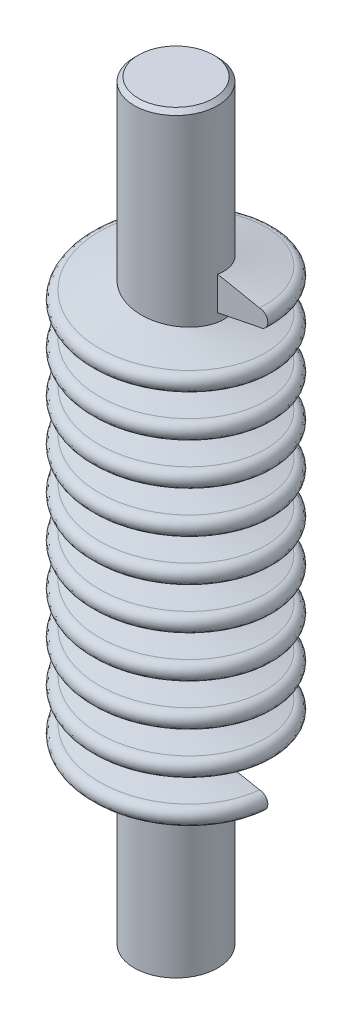
SolidWorks part; units mm, degrees
ref_plane "Front Plane" through (0, 0, 0) normal (0, 0, 1) x (1, 0, 0)
ref_plane "Top Plane" through (0, 0, 0) normal (0, 1, 0) x (1, 0, 0)
ref_plane "Right Plane" through (0, 0, 0) normal (1, 0, 0) x (0, 0, -1)
sketch "Sketch1" plane through (0, 0, 0) normal (0, 1, 0) x (1, 0, 0)
  circle A0 centre (0, 0) radius 5
  dimension "D1" = 10
extrude "Boss-Extrude2" add sketch "Sketch1" along normal blind 90
chamfer "Chamfer1" distance 0.5 angle 45 1 edges at (0, 90, 5)
ref_plane "Plane1" through (0, 70, 0) normal (0, 1, 0) x (1, 0, 0)
sketch "Sketch3" plane through (0, 70, 0) normal (0, 1, 0) x (1, 0, 0)
  circle A0 centre (0, 0) radius 5 construction
  circle A1 centre (0, 0) radius 5
curve "Helix/Spiral1" pitch 5 height 50 turns 10
sketch "Sketch4" plane through (0, 0, 0) normal (0, 0, 1) x (1, 0, 0)
  line L0 (5, 70) -> (6.3876, 70) construction
  line L1 (4.95, 70) -> (-4.95, 70) construction
  line L2 (5, 0) -> (5, 89.5) construction
  line L3 (4.781, 72) -> (5, 72)
  line L4 (4.781, 72) -> (4.781, 68)
  line L5 (4.781, 68) -> (5, 68)
  line L7 (5, 72) -> (10, 71)
  line L8 (5, 68) -> (10, 69)
  arc A0 (10, 69) -> (10, 71) centre (10, 70) ccw
  spline S0 degree 3 poles (5, 70) (5, 69.8965) (4.7397, 69.6872) (3.6276, 69.3751) (1.9632, 69.0625) (0, 68.75) (-1.9632, 68.4375) (-3.6276, 68.125) (-4.7397, 67.8125) (-5.1302, 67.5) (-4.7397, 67.1875) (-3.6276, 66.875) (-1.4084, 66.4583) (1.4084, 66.0417) (3.6276, 65.625) (4.7397, 65.3125) (5.1302, 65) (4.7397, 64.6875) (3.6276, 64.375) (1.4084, 63.9583) (-1.4084, 63.5417) (-3.6276, 63.125) (-4.7397, 62.8125) (-5.1302, 62.5) (-4.7397, 62.1875) (-3.6276, 61.875) (-1.4084, 61.4583) (1.4084, 61.0417) (3.6276, 60.625) (4.7397, 60.3125) (5.1302, 60) (4.7397, 59.6875) (3.6276, 59.375) (1.4084, 58.9583) (-1.4084, 58.5417) (-3.6276, 58.125) (-4.7397, 57.8125) (-5.1302, 57.5) (-4.7397, 57.1875) (-3.6276, 56.875) (-1.4084, 56.4583) (1.4084, 56.0417) (3.6276, 55.625) (4.7397, 55.3125) (5.1302, 55) (4.7397, 54.6875) (3.6276, 54.375) (1.4084, 53.9583) (-1.4084, 53.5417) (-3.6276, 53.125) (-4.7397, 52.8125) (-5.1302, 52.5) (-4.7397, 52.1875) (-3.6276, 51.875) (-1.4084, 51.4583) (1.4084, 51.0417) (3.6276, 50.625) (4.7397, 50.3125) (5.1302, 50) (4.7397, 49.6875) (3.6276, 49.375) (1.4084, 48.9583) (-1.4084, 48.5417) (-3.6276, 48.125) (-4.7397, 47.8125) (-5.1302, 47.5) (-4.7397, 47.1875) (-3.6276, 46.875) (-1.4084, 46.4583) (1.4084, 46.0417) (3.6276, 45.625) (4.7397, 45.3125) (5.1302, 45) (4.7397, 44.6875) (3.6276, 44.375) (1.4084, 43.9583) (-1.4084, 43.5417) (-3.6276, 43.125) (-4.7397, 42.8125) (-5.1302, 42.5) (-4.7397, 42.1875) (-3.6276, 41.875) (-1.4084, 41.4583) (1.4084, 41.0417) (3.6276, 40.625) (4.7397, 40.3125) (5.1302, 40) (4.7397, 39.6875) (3.6276, 39.375) (1.4084, 38.9583) (-1.4084, 38.5417) (-3.6276, 38.125) (-4.7397, 37.8125) (-5.1302, 37.5) (-4.7397, 37.1875) (-3.6276, 36.875) (-1.4084, 36.4583) (1.4084, 36.0417) (3.6276, 35.625) (4.7397, 35.3125) (5.1302, 35) (4.7397, 34.6875) (3.6276, 34.375) (1.4084, 33.9583) (-1.4084, 33.5417) (-3.6276, 33.125) (-4.7397, 32.8125) (-5.1302, 32.5) (-4.7397, 32.1875) (-3.6276, 31.875) (-1.4084, 31.4583) (1.4084, 31.0417) (3.6276, 30.625) (4.7397, 30.3125) (5.1302, 30) (4.7397, 29.6875) (3.6276, 29.375) (1.4084, 28.9583) (-1.4084, 28.5417) (-3.6276, 28.125) (-4.7397, 27.8125) (-5.1302, 27.5) (-4.7397, 27.1875) (-3.6276, 26.875) (-1.4084, 26.4583) (1.4084, 26.0417) (3.6276, 25.625) (4.7397, 25.3125) (5.1302, 25) (4.7397, 24.6875) (3.6276, 24.375) (1.4084, 23.9583) (-1.4084, 23.5417) (-3.6276, 23.125) (-4.7397, 22.8125) (-5.1302, 22.5) (-4.7397, 22.1875) (-3.6276, 21.875) (-1.9632, 21.5625) (0, 21.25) (1.9632, 20.9375) (3.6276, 20.6249) (4.7397, 20.3128) (5, 20.1035) (5, 20) knots 0 0 0 0 0.00625 0.0125 0.01875 0.025 0.03125 0.0375 0.04375 0.05 0.05625 0.0625 0.06875 0.08125 0.0875 0.09375 0.1 0.10625 0.1125 0.11875 0.13125 0.1375 0.14375 0.15 0.15625 0.1625 0.16875 0.18125 0.1875 0.19375 0.2 0.20625 0.2125 0.21875 0.23125 0.2375 0.24375 0.25 0.25625 0.2625 0.26875 0.28125 0.2875 0.29375 0.3 0.30625 0.3125 0.31875 0.33125 0.3375 0.34375 0.35 0.35625 0.3625 0.36875 0.38125 0.3875 0.39375 0.4 0.40625 0.4125 0.41875 0.43125 0.4375 0.44375 0.45 0.45625 0.4625 0.46875 0.48125 0.4875 0.49375 0.5 0.50625 0.5125 0.51875 0.53125 0.5375 0.54375 0.55 0.55625 0.5625 0.56875 0.58125 0.5875 0.59375 0.6 0.60625 0.6125 0.61875 0.63125 0.6375 0.64375 0.65 0.65625 0.6625 0.66875 0.68125 0.6875 0.69375 0.7 0.70625 0.7125 0.71875 0.73125 0.7375 0.74375 0.75 0.75625 0.7625 0.76875 0.78125 0.7875 0.79375 0.8 0.80625 0.8125 0.81875 0.83125 0.8375 0.84375 0.85 0.85625 0.8625 0.86875 0.88125 0.8875 0.89375 0.9 0.90625 0.9125 0.91875 0.93125 0.9375 0.94375 0.95 0.95625 0.9625 0.96875 0.975 0.98125 0.9875 0.99375 1 1 1 1 construction
  dimension "1" = 1
  dimension "D1" = 4
  dimension "D2" = 2
  dimension "D3" = 5
sweep "Sweep1" add profiles "Sketch4" path "Helix/Spiral1"
